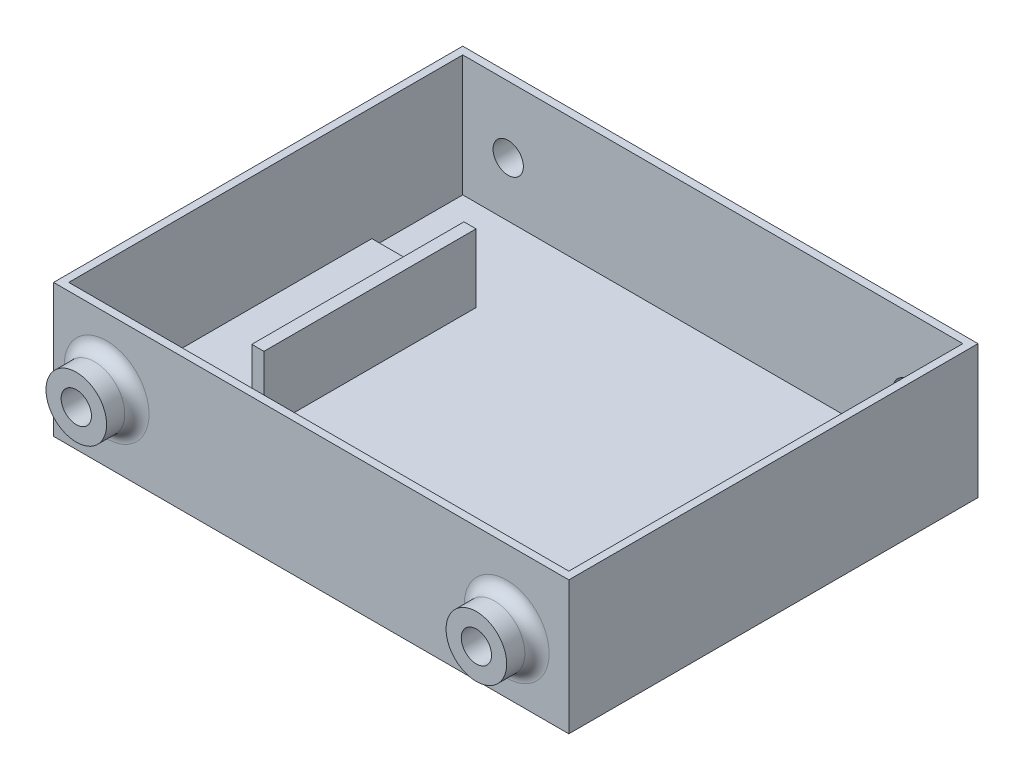
SolidWorks part; units mm, degrees
ref_plane "Front Plane" through (0, 0, 0) normal (0, 0, 1) x (1, 0, 0)
ref_plane "Top Plane" through (0, 0, 0) normal (0, 1, 0) x (1, 0, 0)
ref_plane "Right Plane" through (0, 0, 0) normal (1, 0, 0) x (0, 0, -1)
sketch "Sketch1" plane through (0, 0, 0) normal (0, 1, 0) x (1, 0, 0)
  line L1 (0, 0) -> (107.95, 0)
  line L2 (0, 0) -> (0, 85.725)
  line L3 (0, 85.725) -> (107.95, 85.725)
  line L4 (107.95, 0) -> (107.95, 85.725)
  dimension "D1" = 85.725
  dimension "D2" = 107.95
extrude "Boss-Extrude1" add sketch "Sketch1" along normal blind 2.54 contours L3 L4 L1 L2
sketch "Sketch2" plane through (0, 2.54, 0) normal (0, 1, 0) x (1, 0, 0)
  line L0 (0, 85.725) -> (107.95, 85.725) construction
  line L1 (1.5875, 84.1375) -> (106.3625, 84.1375)
  line L2 (1.5875, 84.1375) -> (1.5875, 1.5875)
  line L3 (1.5875, 1.5875) -> (106.3625, 1.5875)
  line L4 (106.3625, 84.1375) -> (106.3625, 1.5875)
  line L5 (0, 0) -> (0, 85.725) construction
  line L6 (107.95, 0) -> (107.95, 85.725) construction
  line L7 (0, 0) -> (107.95, 0) construction
  line M5 (0, 85.725) -> (0, 0)
  line M6 (0, 0) -> (107.95, 0)
  line M7 (107.95, 0) -> (107.95, 85.725)
  line M8 (107.95, 85.725) -> (0, 85.725)
  dimension "D1" = 1.5875
  dimension "D2" = 1.5875
  dimension "D3" = 1.5875
  dimension "D4" = 1.5875
extrude "Boss-Extrude2" add sketch "Sketch2" along normal blind 25.4 contours L1 L4 L3 L2 M8 M5 M6 M7 | L4 L1 L2 L3
sketch "Sketch3" plane through (0, 0, -85.725) normal (0, 0, -1) x (-1, 0, 0)
  line L0 (0, 27.94) -> (0, 0) construction
  circle A0 centre (-11.1125, 14.0282) radius 3.175
  dimension "D1" = 6.35
  dimension "D2" = 11.1125
extrude "Cut-Extrude1" cut sketch "Sketch3" against normal through all both and the other way through all
sketch "Sketch4" plane through (0, 0, -85.725) normal (0, 0, -1) x (-1, 0, 0)
  circle A0 centre (-94.9325, 12.5147) radius 3.175
  circle A1 centre (-11.1125, 14.0282) radius 3.175 construction
  dimension "D1" = 6.35
  dimension "D2" = 83.82
extrude "Cut-Extrude2" cut sketch "Sketch4" against normal through all both and the other way through all
sketch "Sketch5" plane through (0, 2.54, 0) normal (0, 1, 0) x (1, 0, 0)
  line L0 (1.5875, 84.1375) -> (1.5875, 1.5875) construction
  line L1 (23.4315, 20.6375) -> (1.5875, 20.6375)
  line L2 (23.4315, 20.6375) -> (23.4315, 65.0875)
  line L3 (23.4315, 65.0875) -> (1.5875, 65.0875)
  line L4 (1.5875, 20.6375) -> (1.5875, 65.0875)
  line L5 (1.5875, 1.5875) -> (106.3625, 1.5875) construction
  line L6 (1.5875, 84.1375) -> (106.3625, 84.1375) construction
  dimension "D1" = 19.05
  dimension "D2" = 19.05
  dimension "D3" = 21.844
extrude "Boss-Extrude3" add sketch "Sketch5" along normal blind 1.5875
sketch "Sketch6" plane through (0, 4.1275, 0) normal (0, 1, 0) x (1, 0, 0)
  line L0 (23.4315, 65.0875) -> (1.5875, 65.0875) construction
  line L1 (20.8915, 65.0875) -> (23.4315, 65.0875)
  line L2 (20.8915, 65.0875) -> (20.8915, 20.6375)
  line L3 (20.8915, 20.6375) -> (23.4315, 20.6375)
  line L4 (23.4315, 65.0875) -> (23.4315, 20.6375)
  dimension "D1" = 2.54
extrude "Boss-Extrude4" add sketch "Sketch6" along normal blind 12.7 contours L2 L3 L4 L1
sketch "Sketch7" plane through (0, 0, 0) normal (0, 0, 1) x (1, 0, 0)
  circle A0 centre (11.1125, 14.0282) radius 6.35
  dimension "D1" = 12.7
extrude "Boss-Extrude5" add sketch "Sketch7" along normal blind 6.35
sketch "Sketch8" plane through (0, 0, 0) normal (0, 0, 1) x (1, 0, 0)
  circle A0 centre (94.9325, 12.5147) radius 6.35
  dimension "D1" = 12.7
extrude "Boss-Extrude6" add sketch "Sketch8" along normal blind 6.35
fillet "Fillet1" radius 2.54 1 edges at (4.7625, 14.0282, 0)
fillet "Fillet2" radius 2.54 1 edges at (88.5825, 12.5147, 0)
sketch "Sketch9" plane through (0, 0, -85.725) normal (0, 0, -1) x (-1, 0, 0)
  circle A0 centre (-94.9325, 12.5147) radius 6.35
  dimension "D1" = 12.7
extrude "Boss-Extrude7" add sketch "Sketch9" along normal blind 6.35 contours A0
sketch "Sketch10" plane through (0, 0, -85.725) normal (0, 0, -1) x (-1, 0, 0)
  circle A0 centre (-11.1125, 14.0282) radius 6.35
  dimension "D1" = 12.7
extrude "Boss-Extrude8" add sketch "Sketch10" along normal blind 6.35
fillet "Fillet3" radius 2.54 2 edges at (4.7625, 14.0282, -85.725) (88.5825, 12.5147, -85.725)
sketch "Sketch11" plane through (0, 0, -85.725) normal (0, 0, 1) x (1, 0, 0)
  circle A0 centre (94.9325, 12.5147) radius 3.175
extrude "Cut-Extrude4" cut sketch "Sketch11" against normal through all both and the other way through all
sketch "Sketch12" plane through (0, 0, -85.725) normal (0, 0, 1) x (1, 0, 0)
  circle A0 centre (11.1125, 14.0282) radius 3.175
extrude "Cut-Extrude5" cut sketch "Sketch12" against normal through all both and the other way through all
